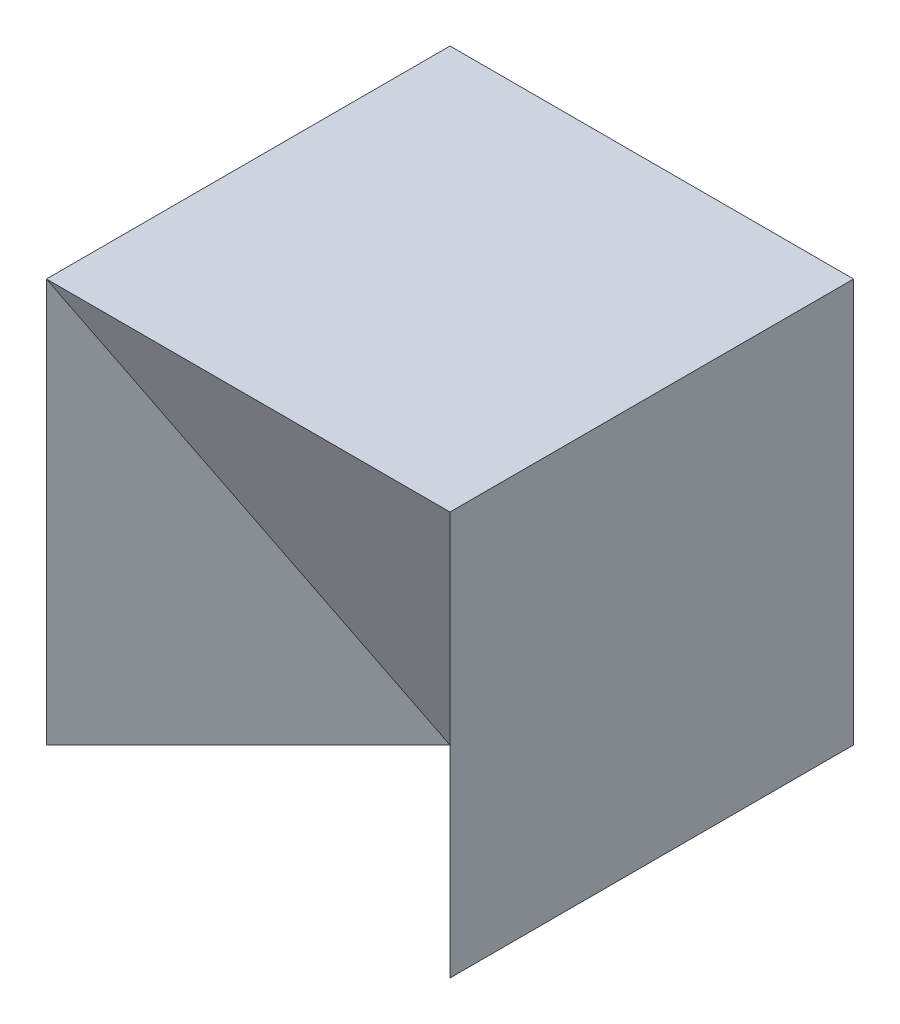
SolidWorks part; units mm, degrees
ref_plane "Front" through (0, 0, 0) normal (0, 0, 1) x (1, 0, 0)
ref_plane "Top" through (0, 0, 0) normal (0, 1, 0) x (1, 0, 0)
ref_plane "Right" through (0, 0, 0) normal (1, 0, 0) x (0, 0, -1)
sketch "Sketch2" plane through (0, 0, 0) normal (0, 1, 0) x (1, 0, 0)
  line L1 (-2, -2) -> (2, -2)
  line L2 (-2, -2) -> (-2, 2)
  line L3 (-2, 2) -> (2, 2)
  line L4 (2, -2) -> (2, 2)
  line L5 (-2, -2) -> (2, 2) construction
  line L6 (-2, 2) -> (2, -2) construction
  point P0 (0, 0)
  dimension "D1" = 4
  dimension "D2" = 4
extrude "Boss-Extrude1" add sketch "Sketch2" along normal blind 4
sketch3d "3DSketch2"
  line L0 (-2, 4, 2) -> (0, 0, 0)
  line L1 (0, 0, 0) -> (2, 4, 2)
  line L2 (2, 4, 2) -> (-2, 4, 2)
extrude "Cut-Extrude2" cut sketch "3DSketch2" along direction (0, -1, 0) on the side of the normal blind 10
